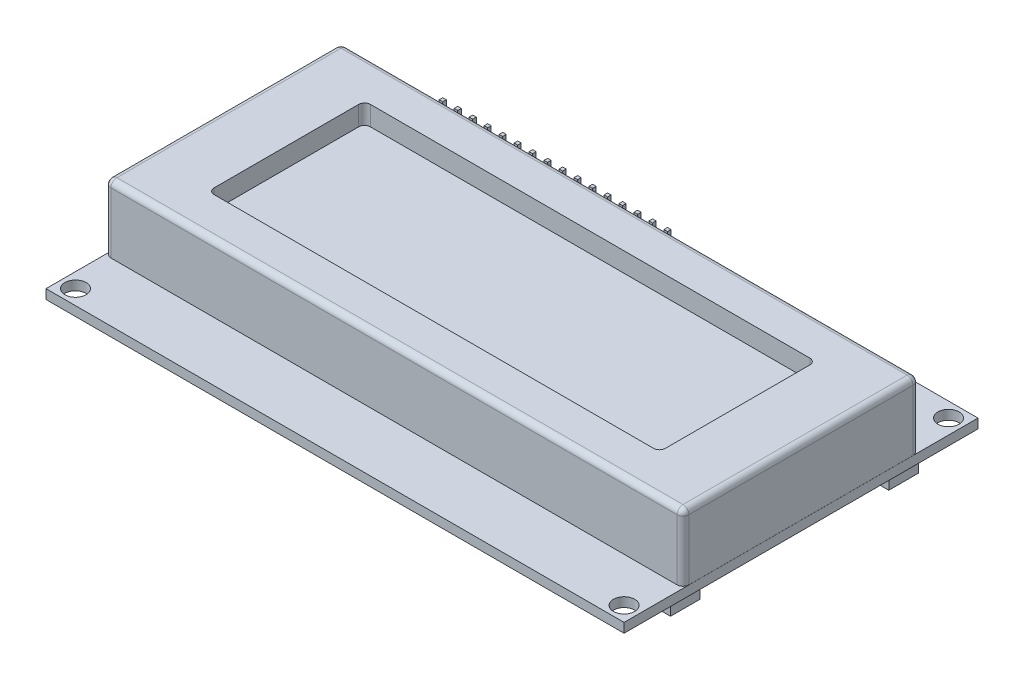
SolidWorks part; units mm, degrees
ref_plane "Front Plane" through (0, 0, 0) normal (0, 0, 1) x (1, 0, 0)
ref_plane "Top Plane" through (0, 0, 0) normal (0, 1, 0) x (1, 0, 0)
ref_plane "Right Plane" through (0, 0, 0) normal (1, 0, 0) x (0, 0, -1)
sketch "Sketch1" plane through (0, 0, 0) normal (0, 1, 0) x (1, 0, 0)
  line L1 (-49, -30) -> (49, -30)
  line L2 (-49, -30) -> (-49, 30)
  line L3 (-49, 30) -> (49, 30)
  line L4 (49, -30) -> (49, 30)
  line L5 (-49, -30) -> (49, 30) construction
  line L6 (-49, 30) -> (49, -30) construction
  point P0 (0, 0)
  dimension "D1" = 98
  dimension "D2" = 60
extrude "Boss-Extrude1" add sketch "Sketch1" along normal blind 1.6
sketch "Sketch2" plane through (0, 1.6, 0) normal (0, 1, 0) x (1, 0, 0)
  line L1 (-46.5, -27.5) -> (46.5, -27.5) construction
  line L2 (-46.5, -27.5) -> (-46.5, 27.5) construction
  line L3 (-46.5, 27.5) -> (46.5, 27.5) construction
  line L4 (46.5, -27.5) -> (46.5, 27.5) construction
  line L5 (-46.5, -27.5) -> (46.5, 27.5) construction
  line L6 (-46.5, 27.5) -> (46.5, -27.5) construction
  circle A0 centre (-46.5, 27.5) radius 1.8
  point P0 (0, 0)
  dimension "D3" = 3.6
  dimension "D1" = 93
  dimension "D2" = 55
extrude "Cut-Extrude1" cut sketch "Sketch2" against normal through all and the other way through all
sketch "Sketch5" plane through (0, 0, 0) normal (0, -1, 0) x (1, 0, 0)
  line L1 (-44.375, -18.5) -> (44.375, -18.5) construction
  line L2 (-44.375, -18.5) -> (-44.375, 18.5) construction
  line L3 (-44.375, 18.5) -> (44.375, 18.5) construction
  line L4 (44.375, -18.5) -> (44.375, 18.5) construction
  line L5 (-44.375, -18.5) -> (44.375, 18.5) construction
  line L6 (-44.375, 18.5) -> (44.375, -18.5) construction
  line L7 (-47.875, 16) -> (-40.875, 16)
  line L8 (-47.875, 16) -> (-47.875, 21)
  line L9 (-47.875, 21) -> (-40.875, 21)
  line L10 (-40.875, 16) -> (-40.875, 21)
  line L11 (-47.875, 16) -> (-40.875, 21) construction
  line L12 (-47.875, 21) -> (-40.875, 16) construction
  line L13 (16, -18.5) -> (-16, -18.5) construction
  line L14 (16, -18.5) -> (16, 18.5) construction
  line L15 (16, 18.5) -> (-16, 18.5) construction
  line L16 (-16, -18.5) -> (-16, 18.5) construction
  line L17 (16, -18.5) -> (-16, 18.5) construction
  line L18 (16, 18.5) -> (-16, -18.5) construction
  line L19 (-19.5, 16) -> (-12.5, 16)
  line L20 (-19.5, 16) -> (-19.5, 21)
  line L21 (-19.5, 21) -> (-12.5, 21)
  line L22 (-12.5, 16) -> (-12.5, 21)
  line L23 (-19.5, 16) -> (-12.5, 21) construction
  line L24 (-19.5, 21) -> (-12.5, 16) construction
  point P0 (0, 0)
  point P10 (0, 0)
  dimension "D1" = 88.75
  dimension "D2" = 37
  dimension "D3" = 7
  dimension "D4" = 5
  dimension "D5" = 32
extrude "Boss-Extrude3" add sketch "Sketch5" along normal blind 2.57
mirror "Mirror1" about plane through (0, 0, 0) normal (0, 0, 1) of "Boss-Extrude3", "Cut-Extrude1"
mirror "Mirror2" about plane through (0, 0, 0) normal (1, 0, 0) of "Mirror1", "Cut-Extrude1", "Boss-Extrude3"
sketch "Sketch3" plane through (0, 1.6, 0) normal (0, 1, 0) x (1, 0, 0)
  line L1 (-48.99, -20) -> (48.99, -20)
  line L2 (-48.99, -20) -> (-48.99, 20)
  line L3 (-48.99, 20) -> (48.99, 20)
  line L4 (48.99, -20) -> (48.99, 20)
  line L5 (-48.99, -20) -> (48.99, 20) construction
  line L6 (-48.99, 20) -> (48.99, -20) construction
  line L7 (49, -30) -> (49, 30) construction
  point P0 (0, 0)
  point P8 (0, 0)
  point P9 (0, 0)
  dimension "D1" = 40
  dimension "D2" = 0.01
extrude "Boss-Extrude2" add sketch "Sketch3" along normal blind 11.3
sketch "Sketch4" plane through (0, 12.9, 0) normal (0, 1, 0) x (1, 0, 0)
  line L1 (-38.25, -13.25) -> (38.25, -13.25)
  line L2 (-38.25, -13.25) -> (-38.25, 13.25)
  line L3 (-38.25, 13.25) -> (38.25, 13.25)
  line L4 (38.25, -13.25) -> (38.25, 13.25)
  line L5 (-38.25, -13.25) -> (38.25, 13.25) construction
  line L6 (-38.25, 13.25) -> (38.25, -13.25) construction
  point P0 (0, 0)
  dimension "D1" = 76.5
  dimension "D2" = 26.5
extrude "Cut-Extrude2" cut sketch "Sketch4" against normal blind 3.3
fillet "Fillet1" radius 1 12 edges at (-38.25, 11.25, 13.25) (38.25, 11.25, 13.25) (38.25, 11.25, -13.25) (-38.25, 11.25, -13.25) (-48.99, 12.9, 0) (0, 12.9, -20) (48.99, 12.9, 0) (0, 12.9, 20) (-48.99, 7.25, 20) (48.99, 7.25, 20) (48.99, 7.25, -20) (-48.99, 7.25, -20)
sketch "Sketch6" plane through (0, 0, 0) normal (0, -1, 0) x (1, 0, 0)
  line L1 (-40.8, -29) -> (6.4, -29)
  line L2 (-40.8, -29) -> (-40.8, -10)
  line L3 (-40.8, -10) -> (6.4, -10)
  line L4 (6.4, -29) -> (6.4, -10)
  line L5 (-40.8, -29) -> (6.4, -10) construction
  line L6 (-40.8, -10) -> (6.4, -29) construction
  line L8 (-49, -30) -> (-49, 30) construction
  line L9 (49, -30) -> (-49, -30) construction
  point P0 (-17.2, -19.5)
  dimension "D1" = 19
  dimension "D2" = 47.2
  dimension "D3" = 8.2
  dimension "D4" = 1
extrude "Boss-Extrude4" add sketch "Sketch6" along normal blind 11.5
sketch "Sketch7" plane through (-40.8, 0, 0) normal (1, 0, 0) x (0, 0, -1)
  line L0 (15.25, -8.8) -> (17.79, -8.8) construction
  line L1 (17.79, -8.8) -> (20.33, -8.8) construction
  line L2 (20.33, -8.8) -> (22.87, -8.8) construction
  line L3 (10, -11.5) -> (10, 0) construction
  line L6 (-30, 0) -> (30, 0) construction
  line L8 (14.95, -9.1) -> (15.55, -9.1)
  line L9 (14.95, -9.1) -> (14.95, -8.5)
  line L10 (14.95, -8.5) -> (15.55, -8.5)
  line L11 (15.55, -9.1) -> (15.55, -8.5)
  line L12 (14.95, -9.1) -> (15.55, -8.5) construction
  line L13 (14.95, -8.5) -> (15.55, -9.1) construction
  line L14 (17.49, -9.1) -> (18.09, -9.1)
  line L15 (17.49, -9.1) -> (17.49, -8.5)
  line L16 (17.49, -8.5) -> (18.09, -8.5)
  line L17 (18.09, -9.1) -> (18.09, -8.5)
  line L18 (17.49, -9.1) -> (18.09, -8.5) construction
  line L19 (17.49, -8.5) -> (18.09, -9.1) construction
  line L20 (20.03, -9.1) -> (20.63, -9.1)
  line L21 (20.03, -9.1) -> (20.03, -8.5)
  line L22 (20.03, -8.5) -> (20.63, -8.5)
  line L23 (20.63, -9.1) -> (20.63, -8.5)
  line L24 (20.03, -9.1) -> (20.63, -8.5) construction
  line L25 (20.03, -8.5) -> (20.63, -9.1) construction
  line L26 (22.57, -9.1) -> (23.17, -9.1)
  line L27 (22.57, -9.1) -> (22.57, -8.5)
  line L28 (22.57, -8.5) -> (23.17, -8.5)
  line L29 (23.17, -9.1) -> (23.17, -8.5)
  line L30 (22.57, -9.1) -> (23.17, -8.5) construction
  line L31 (22.57, -8.5) -> (23.17, -9.1) construction
  dimension "D1" = 2.54
  dimension "D2" = 5.25
  dimension "D3" = 8.8
  dimension "D4" = 0.6
  dimension "D5" = 0.6
extrude "Boss-Extrude5" add sketch "Sketch7" against normal blind 6.5
sketch "Sketch9" plane through (0, 1.6, 0) normal (0, 1, 0) x (1, 0, 0)
  line L0 (-49, 27.46) -> (-39.2, 27.46) construction
  line L1 (-49, 30) -> (-49, -30) construction
  line L2 (-39.2, 27.46) -> (-39.2, 30) construction
  line L3 (49, 30) -> (-49, 30) construction
  line L5 (-39.5, 27.16) -> (-38.9, 27.16)
  line L6 (-39.5, 27.16) -> (-39.5, 27.76)
  line L7 (-39.5, 27.76) -> (-38.9, 27.76)
  line L8 (-38.9, 27.16) -> (-38.9, 27.76)
  line L9 (-39.5, 27.16) -> (-38.9, 27.76) construction
  line L10 (-39.5, 27.76) -> (-38.9, 27.16) construction
  dimension "D1" = 9.8
  dimension "D2" = 2.54
  dimension "D3" = 0.6
extrude "Boss-Extrude7" add sketch "Sketch9" along normal blind 3.9
pattern_linear "LPattern1" count 16 spacing 2.54 along (1, 0, 0) of "Boss-Extrude7"
